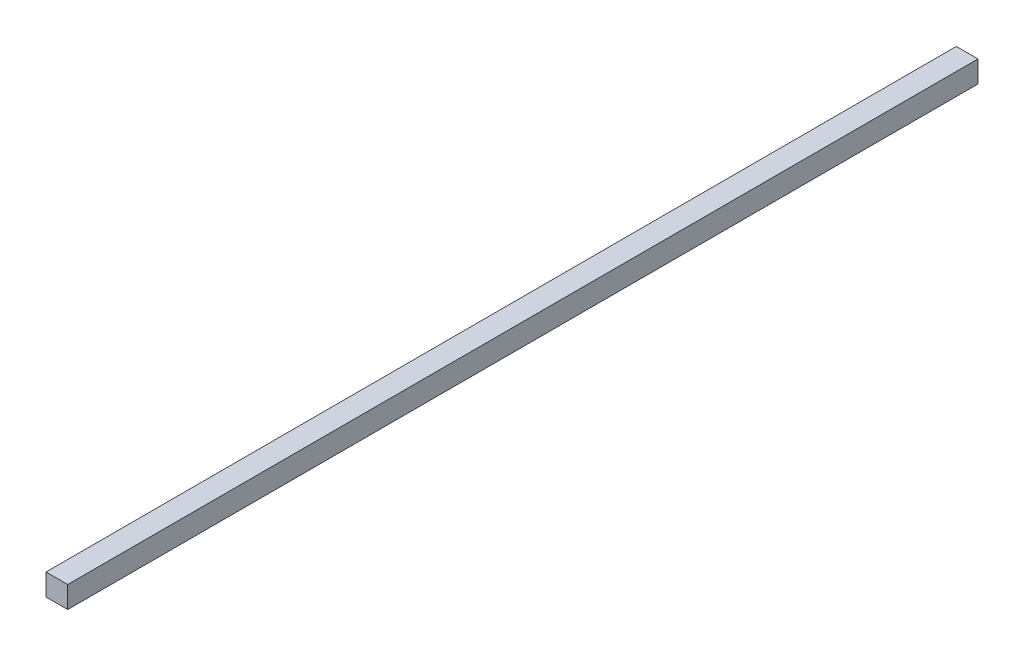
SolidWorks part; units mm, degrees
ref_plane "Front Plane" through (0, 0, 0) normal (0, 0, 1) x (1, 0, 0)
ref_plane "Top Plane" through (0, 0, 0) normal (0, 1, 0) x (1, 0, 0)
ref_plane "Right Plane" through (0, 0, 0) normal (1, 0, 0) x (0, 0, -1)
sketch "Sketch1" plane through (0, 0, 0) normal (0, 1, 0) x (1, 0, 0)
  line L1 (0, 0) -> (25.4, 0)
  line L2 (0, 0) -> (0, 1066.4976)
  line L3 (0, 1066.4976) -> (25.4, 1066.4976)
  line L4 (25.4, 0) -> (25.4, 1066.4976)
  dimension "D1" = 1066.8
  dimension "D2" = 25.4
extrude "Boss-Extrude1" add sketch "Sketch1" along normal blind 25.4
